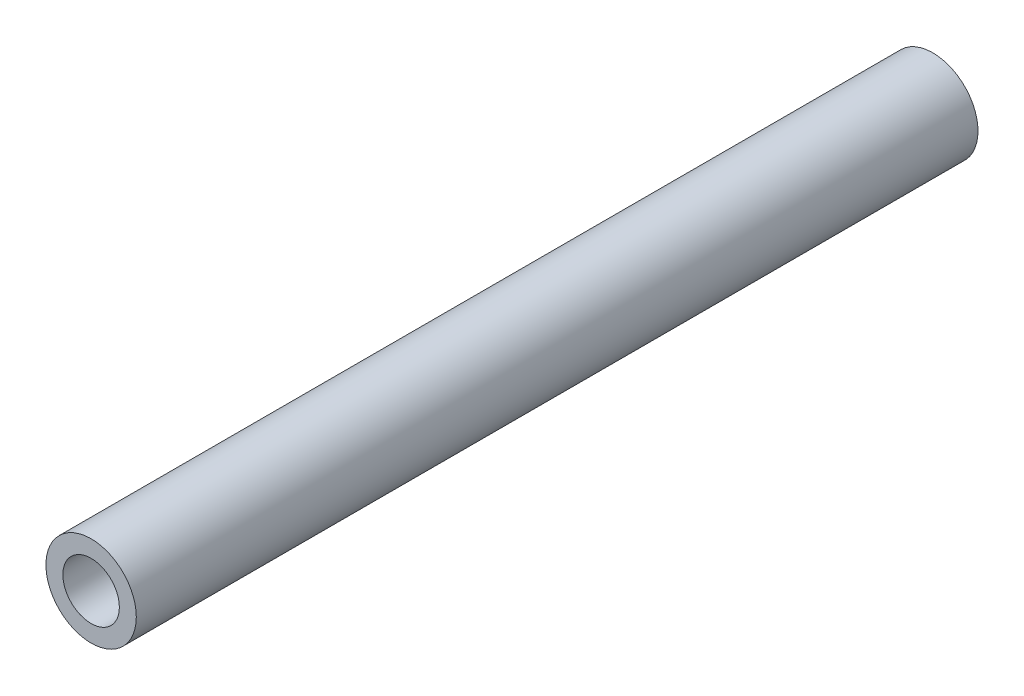
SolidWorks part; units mm, degrees
ref_plane "Front Plane" through (0, 0, 0) normal (0, 0, 1) x (1, 0, 0)
ref_plane "Top Plane" through (0, 0, 0) normal (0, 1, 0) x (1, 0, 0)
ref_plane "Right Plane" through (0, 0, 0) normal (1, 0, 0) x (0, 0, -1)
sketch "Sketch1" plane through (0, 0, 0) normal (0, 0, 1) x (1, 0, 0)
  circle A0 centre (0, 0) radius 4
extrude "Boss-Extrude1" add sketch "Sketch1" along normal blind 74.5
sketch "Sketch2" plane through (0, 0, 74.5) normal (0, 0, 1) x (1, 0, 0)
  circle A0 centre (0, 0) radius 2.5
extrude "Cut-Extrude1" cut sketch "Sketch2" against normal blind 16
